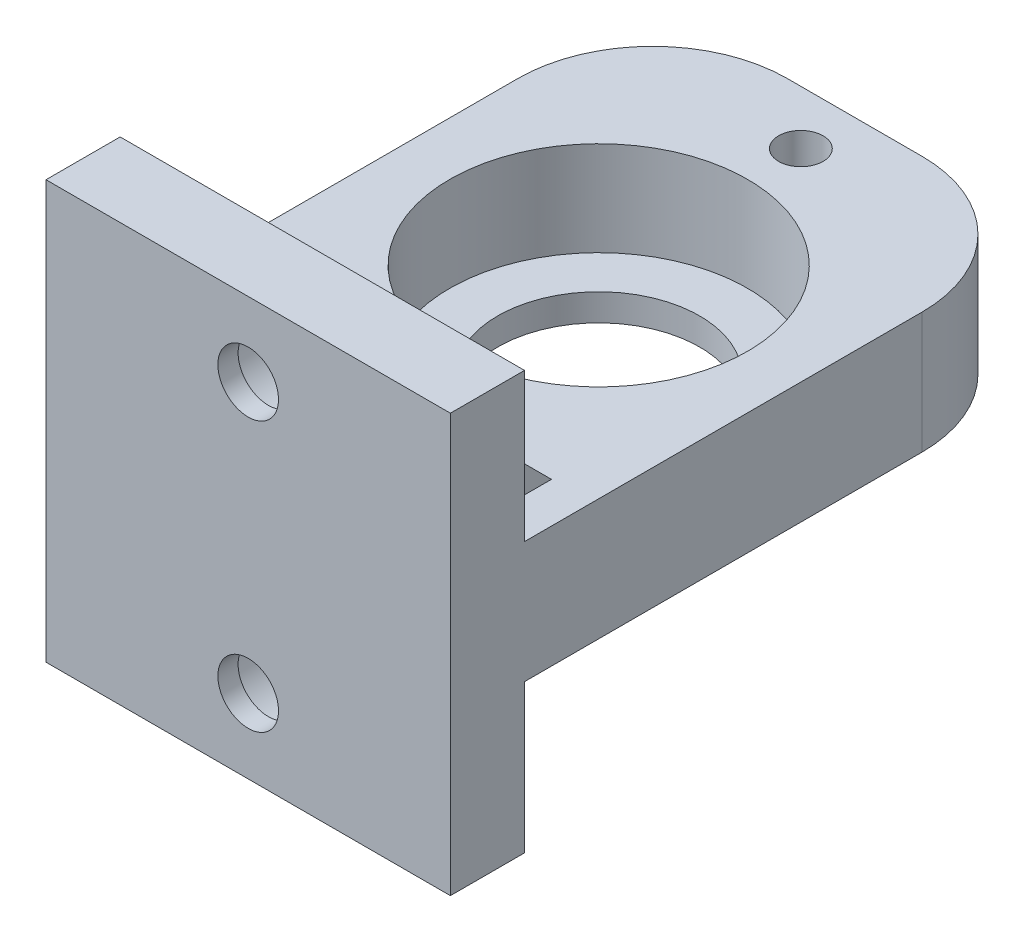
SolidWorks part; units mm, degrees
material "ABS"
ref_plane "Front Plane" through (0, 0, 0) normal (0, 0, 1) x (1, 0, 0)
ref_plane "Top Plane" through (0, 0, 0) normal (0, 1, 0) x (1, 0, 0)
ref_plane "Right Plane" through (0, 0, 0) normal (1, 0, 0) x (0, 0, -1)
sketch "Sketch2" plane through (0, 0, 0) normal (0, 1, 0) x (1, 0, 0)
  line L1 (-15, 22.5) -> (15, 22.5)
  line L2 (-15, 22.5) -> (-15, -22.5)
  line L3 (-15, -22.5) -> (15, -22.5)
  line L4 (15, 22.5) -> (15, -22.5)
  line L5 (-15, 22.5) -> (15, -22.5) construction
  line L6 (-15, -22.5) -> (15, 22.5) construction
  point P0 (0, 0)
  dimension "D1" = 30
  dimension "D2" = 45
extrude "Boss-Extrude1" add sketch "Sketch2" along normal blind 9
sketch "Sketch3" plane through (0, 9, 0) normal (0, 1, 0) x (1, 0, 0)
  line L0 (-15, -22.5) -> (15, -22.5) construction
  circle A0 centre (0, 3.5) radius 11.05
  point P6 (0, 0)
  dimension "D1" = 22.1
  dimension "D2" = 26
extrude "Cut-Extrude1" cut sketch "Sketch3" against normal blind 7
sketch "Sketch4" plane through (0, 2, 0) normal (0, 1, 0) x (1, 0, 0)
  circle A0 centre (0, 3.5) radius 7.5
  point P5 (0, 3.5)
  dimension "D1" = 15
extrude "Cut-Extrude2" cut sketch "Sketch4" against normal through all
fillet "Fillet1" radius 10 2 edges at (15, 4.5, -22.5) (-15, 4.5, -22.5)
sketch "Sketch5" plane through (0, 0, 22.5) normal (0, 0, 1) x (1, 0, 0)
  line L0 (15, 9) -> (15, 0) construction
  line L1 (-15, 0) -> (15, 0)
  line L2 (-15, 0) -> (-15, -11)
  line L3 (-15, -11) -> (15, -11)
  line L4 (15, 0) -> (15, -11)
  line L5 (-15, 9) -> (15, 9) construction
  dimension "D1" = 20
extrude "Boss-Extrude2" add sketch "Sketch5" against normal blind 5.5
sketch "Sketch6" plane through (0, 0, 17) normal (0, 0, -1) x (-1, 0, 0)
  line L0 (0, 0) -> (0, -11) construction
  line L1 (-15, 0) -> (15, 0) construction
  line L2 (15, -11) -> (-15, -11) construction
  point P6 (0, -5.5)
hole_wizard "CBORE for M4 SHCS1" positions "Sketch11" profile "Sketch8" counterbore size "M4" standard "ANSI Metric" end condition through all
sketch "Sketch11" plane through (0, 0, 17) normal (0, 0, -1) x (-1, 0, 0)
  point P0 (0, -5.5)
sketch "Sketch8" plane through (0, -5.5, 17) normal (1, 0, 0) x (0, 1, 0)
  line L0 (0, 0) -> (0, 5.5)
  line L1 (0, 5.5) -> (2.25, 5.5)
  line L3 (2.25, 5.5) -> (2.25, 4)
  line L4 (2.25, 4) -> (4, 4)
  line L5 (4, 4) -> (4, 0)
  line L7 (4, 0) -> (0, 0)
  line L11 (0, -6.35) -> (0, 107.95) construction
  dimension "Thru Hole Dia." = 4.5
  dimension "Thru Hole Depth" = 5.5
  dimension "C'Bore Dia." = 8
  dimension "C'Bore Depth" = 4
ref_plane "Plane1" through (-10, 0, 0) normal (-1, 0, 0) x (0, 0, 1)
sketch "Sketch10" plane through (-10, 0, 0) normal (-1, 0, 0) x (0, 0, 1)
  line L0 (12, 0) -> (17, -5)
  line L1 (-12.5, 0) -> (17, 0) construction
  line L2 (17, 0) -> (17, -11) construction
  dimension "D1" = 5
  dimension "D2" = 5
rib "Rib1" sketch "Sketch10" sketch "Sketch10" thickness 4 extrusion direction parallel to sketch draft on no parameters "D1"=4
mirror "Mirror1" about plane through (0, 0, 0) normal (1, 0, 0) of "Rib1"
chamfer "Chamfer1" [suppressed] distance 2 angle 45
sketch "Sketch12" plane through (0, 9, 0) normal (0, 1, 0) x (1, 0, 0)
  line L0 (0, 22.5) -> (0, -22.5) construction
  line L1 (5, 22.5) -> (-5, 22.5) construction
  line L2 (-15, -22.5) -> (15, -22.5) construction
  line L3 (0, 3.5) -> (6.5137, 3.5) construction
  circle A0 centre (0, 3.5) radius 7.5 construction
  circle A1 centre (0, 3.5) radius 7.5 construction
  point P6 (0, 3.5)
  point P11 (0, 18.5)
  point P12 (0, -11.5)
  dimension "D1" = 30
hole_wizard "Ø3.3 (3.3) Diameter Hole1" positions "Sketch12" profile "Sketch13" hole size "Ø3.3" standard "ANSI Metric"
sketch "Sketch13" plane through (0, 9, 11.5) normal (1, 0, 0) x (0, 0, 1)
  line L0 (0, 0) -> (0, 5.9914)
  line L1 (0, 5.9914) -> (1.65, 5)
  line L2 (1.65, 5) -> (1.65, 0)
  line L5 (1.65, 0) -> (0, 0)
  line L10 (0, 5.9914) -> (-1.65, 5) construction
  line L11 (0, -6.35) -> (0, 107.95) construction
  dimension "Hole Dia." = 3.3
  dimension "Hole Depth" = 5
  dimension "Drill Angle" = 118
sketch "Sketch14" plane through (0, 9, 0) normal (0, 1, 0) x (1, 0, 0)
  line L0 (-15, 12.5) -> (-15, -22.5) construction
  line L1 (-15, -17) -> (15, -17)
  line L2 (-15, -17) -> (-15, -22.5)
  line L3 (-15, -22.5) -> (15, -22.5)
  line L4 (15, -17) -> (15, -22.5)
  line L5 (-15, -17) -> (15, -17) construction
extrude "Boss-Extrude3" add sketch "Sketch14" along normal blind 11
ref_plane "Plane2" through (0, 4.5, 0) normal (0, -1, 0) x (-1, 0, 0)
mirror "Mirror2" about plane through (0, 4.5, 0) normal (0, -1, 0) of "Mirror1", "Rib1"
mirror "Mirror3" about plane through (0, 4.5, 0) normal (0, -1, 0) of "CBORE for M4 SHCS1"
